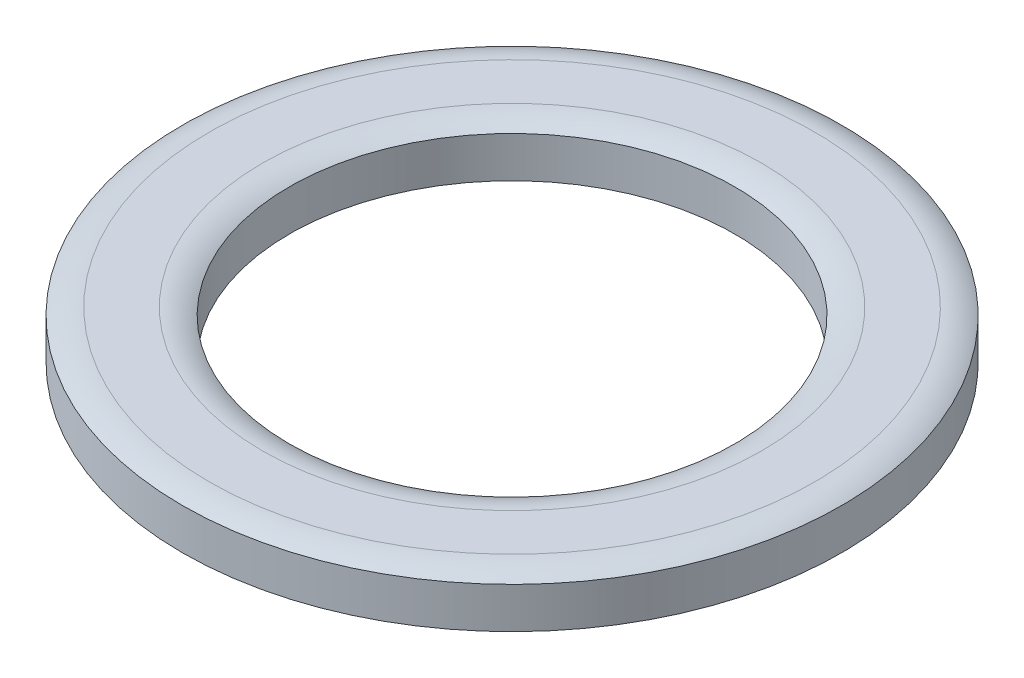
SolidWorks part; units mm, degrees
ref_plane "Front Plane" through (0, 0, 0) normal (0, 0, 1) x (1, 0, 0)
ref_plane "Top Plane" through (0, 0, 0) normal (0, 1, 0) x (1, 0, 0)
ref_plane "Right Plane" through (0, 0, 0) normal (1, 0, 0) x (0, 0, -1)
sketch "Sketch1" plane through (0, 0, 0) normal (0, 1, 0) x (1, 0, 0)
  circle A0 centre (0, 0) radius 5.5626
  circle A1 centre (0, 0) radius 3.7592
  dimension "OD" = 11.1252
  dimension "ID" = 7.5184
sketch "Sketch2" plane through (0, 0, 0) normal (1, 0, 0) x (0, 0, -1)
  line L0 (5.5626, 0.4064) -> (5.5626, -0.4064) construction
  line L1 (0, 0.4064) -> (0, -0.4064) construction
  point P2 (5.5626, 0)
  dimension "Thickness Range" = 0.8128
sketch "Sketch3" plane through (0, 0, 0) normal (1, 0, 0) x (0, 0, -1)
  line L0 (5.5626, -0.4064) -> (3.7592, -0.4064)
  line L1 (3.7592, -0.4064) -> (3.7592, 0.2845)
  line L2 (5.5626, -0.4064) -> (5.5626, 0.2845)
  line L3 (5.5626, 0.4064) -> (5.5626, -0.4064) construction
  line L4 (5.5626, 0.4064) -> (3.7592, 0.4064) construction
  line L5 (3.7592, 0.4064) -> (3.7592, -0.4064) construction
  line L6 (4.2101, 0.4064) -> (5.1118, 0.4064)
  line L7 (3.7592, -0.061) -> (4.2101, -0.061) construction
  line L8 (4.2101, -0.061) -> (4.6609, -0.061) construction
  line L9 (4.6609, -0.061) -> (5.1118, -0.061) construction
  line L10 (5.1118, -0.061) -> (5.5626, -0.061) construction
  arc A1 (4.2101, 0.4064) -> (3.7592, 0.2845) centre (4.21, -0.4882) ccw
  arc A2 (5.1118, 0.4064) -> (5.5626, 0.2845) centre (5.1118, -0.4882) cw
  point P12 (3.7592, 0)
  point P14 (4.6609, 0.4064)
  dimension "D1" = 0.6909
revolve "Revolve1" add sketch "Sketch3" angle 360 about L1
equation "\"D1@Sketch3\"=\"Thickness Range@Sketch2\"*.85"
